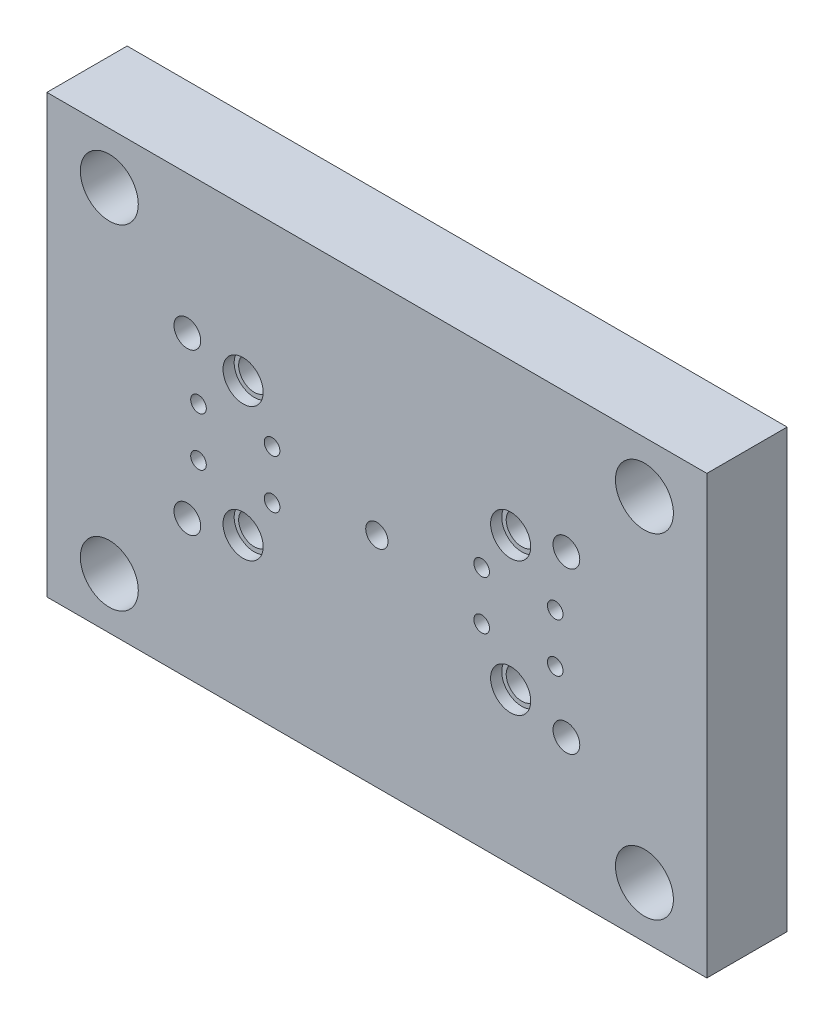
SolidWorks part; units mm, degrees
ref_plane "Front Plane" through (0, 0, 0) normal (0, 0, 1) x (1, 0, 0)
ref_plane "Top Plane" through (0, 0, 0) normal (0, 1, 0) x (1, 0, 0)
ref_plane "Right Plane" through (0, 0, 0) normal (1, 0, 0) x (0, 0, -1)
sketch "Sketch1" plane through (0, 0, 0) normal (0, 0, 1) x (1, 0, 0)
  line L0 (148, 98) -> (-148, 98) construction
  line L1 (148, -98) -> (-148, -98)
  line L2 (148, -98) -> (148, 98)
  line L3 (148, 98) -> (-148, 98)
  line L4 (-148, -98) -> (-148, 98)
  line L5 (148, -98) -> (-148, 98) construction
  line L6 (148, 98) -> (-148, -98) construction
  line L7 (-148, 98) -> (-148, -98) construction
  line L8 (-44.75, 10.94) -> (-49.25, 10.94) construction
  line L9 (-44.75, 11.54) -> (-44.75, 10.34) construction
  line L10 (-49.25, 10.34) -> (-49.25, 11.54) construction
  line L11 (-77.75, 10.94) -> (-82.25, 10.94) construction
  line L12 (-77.75, 11.54) -> (-77.75, 10.34) construction
  line L13 (-82.25, 10.34) -> (-82.25, 11.54) construction
  line L14 (0, 0) -> (-121.4594, 0) construction
  line L15 (0, 0) -> (0, 53.7938) construction
  circle A0 centre (-120, 75) radius 13 construction
  circle A1 centre (-120, -75) radius 13 construction
  circle A2 centre (120, 75) radius 13 construction
  circle A3 centre (120, -75) radius 13 construction
  circle A4 centre (-120, 75) radius 13
  circle A5 centre (-120, -75) radius 13
  circle A6 centre (120, 75) radius 13
  circle A7 centre (120, -75) radius 13
  circle A8 centre (-47, 10.94) radius 3.5
  circle A9 centre (-80, 10.94) radius 3.5
  circle A10 centre (-80, -10.94) radius 3.5
  circle A11 centre (-47, -10.94) radius 3.5
  circle A12 centre (47, -10.94) radius 3.5
  circle A13 centre (80, -10.94) radius 3.5
  circle A14 centre (80, 10.94) radius 3.5
  circle A15 centre (47, 10.94) radius 3.5
  circle A16 centre (-85, 36) radius 6
  circle A17 centre (-85, -36) radius 6
  circle A18 centre (85, 36) radius 6
  circle A19 centre (85, -36) radius 6
  circle A20 centre (0, 0) radius 5
  point P0 (0, 0)
  dimension "D1" = 7
  dimension "D2" = 12
  dimension "D3" = 10
extrude "Extrude1" add sketch "Sketch1" against normal blind 36
hole_wizard "CBORE for 14 mm Core Pins1" positions "Sketch3" profile "Sketch2" counterbore size "14" standard "HASCO Metric" end condition through all
sketch "Sketch3" plane through (0, 0, 0) normal (0, 0, 1) x (1, 0, 0)
  line L0 (0, 0) -> (113.4289, 0) construction
  line L1 (0, 0) -> (0, 71.2541) construction
  point P0 (60, 30)
  point P11 (-60, 30)
  point P12 (-60, -30)
  point P13 (60, -30)
  dimension "D1" = 60
  dimension "D2" = 30
sketch "Sketch2" plane through (60, 30, 0) normal (1, 0, 0) x (0, -1, 0)
  line L0 (0, 0) -> (0, 36)
  line L1 (0, 36) -> (7, 36)
  line L3 (7, 36) -> (7, 5)
  line L4 (7, 5) -> (9, 5)
  line L5 (9, 5) -> (9, 0)
  line L7 (9, 0) -> (0, 0)
  line L11 (0, -6.35) -> (0, 107.95) construction
  dimension "Диаметр сквозного отверстия" = 14
  dimension "Глубина сквозного отверстия" = 36
  dimension "Диаметр цековки" = 18
  dimension "Глубина цековки" = 5
